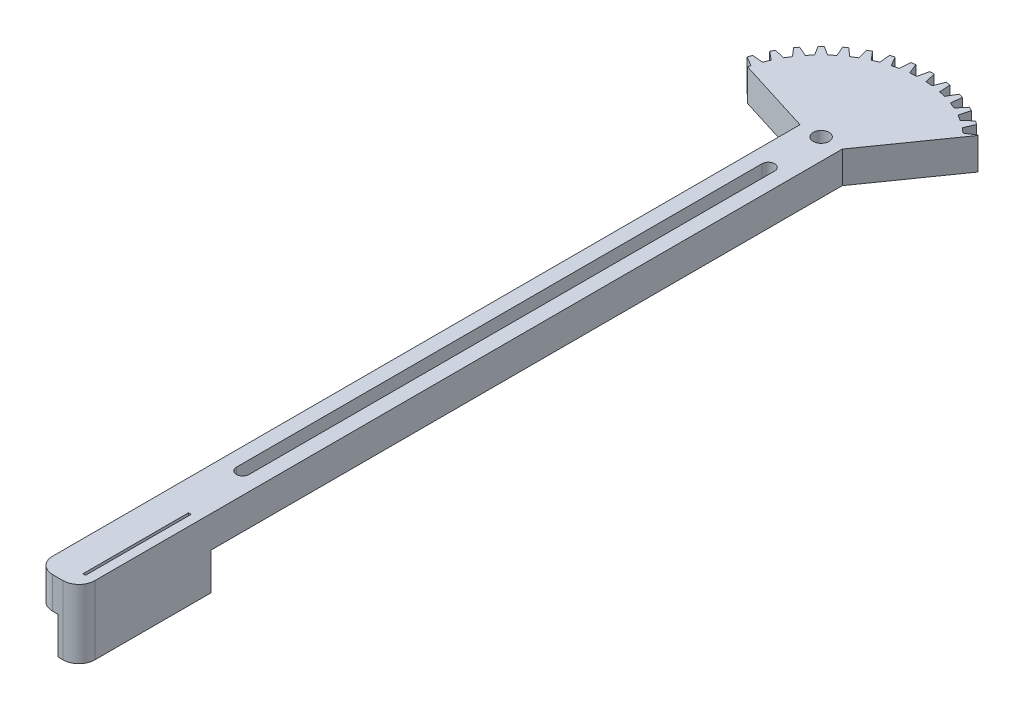
SolidWorks part; units mm, degrees
material "PBT General Purpose"
ref_plane "Front Plane" through (0, 0, 0) normal (0, 0, 1) x (1, 0, 0)
ref_plane "Top Plane" through (0, 0, 0) normal (0, 1, 0) x (1, 0, 0)
ref_plane "Right Plane" through (0, 0, 0) normal (1, 0, 0) x (0, 0, -1)
sketch "Sketch1" plane through (0, 0, 0) normal (0, 1, 0) x (1, 0, 0)
  circle A0 centre (0, 0) radius 21
  circle A1 centre (0, 0) radius 1.5
  dimension "D2" = 3
  dimension "D1" = 42
extrude "Boss-Extrude1" add sketch "Sketch1" along normal blind 6
sketch "Sketch2" plane through (0, 6, 0) normal (0, 1, 0) x (1, 0, 0)
  line L0 (0, 0) -> (0, 15.5) construction
  line L1 (0, 0) -> (-0.4123, 20.996) construction
  line L2 (0, 0) -> (-0.8702, 18.9801) construction
  line L3 (0, 0) -> (-1.4907, 18.9414) construction
  line L4 (-0.8702, 18.9801) -> (-0.4123, 20.996)
  line L5 (0.8702, 18.9801) -> (0.4123, 20.996)
  line L6 (-1.4907, 18.9414) -> (-1.7314, 22)
  line L7 (1.4907, 18.9414) -> (1.7314, 22)
  line L8 (-1.7314, 22) -> (1.7314, 22)
  arc A0 (-0.8702, 18.9801) -> (-1.4907, 18.9414) centre (0, 0) ccw
  circle A1 centre (0, 0) radius 21 construction
  arc A2 (0.4123, 20.996) -> (-0.4123, 20.996) centre (0, 0) ccw
  arc A3 (0.8702, 18.9801) -> (1.4907, 18.9414) centre (0, 0) cw
  dimension "D1" = 19
  dimension "D2" = 1.125
  dimension "D3" = 1.5
  dimension "D4" = 1.875
  dimension "D5" = 22
extrude "Cut-Extrude1" cut sketch "Sketch2" against normal up to next (6 mm away)
pattern_circular "CirPattern1" count 40 over 360 about axis through (0, 0, 0) along (0, 1, 0) of "Cut-Extrude1"
sketch "Sketch3" plane through (0, 6, 0) normal (0, 1, 0) x (1, 0, 0)
  line L0 (4, 0) -> (-4, 0) construction
  line L1 (0, 0) -> (0, 21.0096) construction
  line L2 (0, 0) -> (-26.0972, 6.5552) construction
  line L3 (-4, 0) -> (-20.3673, 5.1159)
  line L4 (-4, 0) -> (4, 0)
  line L6 (0, 0) -> (-7.8504, 27.559) construction
  line L7 (0, 0) -> (15.7913, 16.2954) construction
  line L8 (4, 0) -> (14.6142, 15.0807)
  arc A0 (-20.3673, 5.1159) -> (14.6142, 15.0807) centre (0, 0) ccw
  point P5 (0, 0)
  dimension "D3" = 21
  dimension "D1" = 8
  dimension "D2" = 60
  dimension "D4" = 15.9
  dimension "D5" = 120
extrude "Cut-Extrude2" cut sketch "Sketch3" against normal up to next
sketch "Sketch4" plane through (0, 0, 0) normal (0, -1, 0) x (1, 0, 0)
  line L0 (1.5, 0) -> (4, 0)
  line L1 (-4, 0) -> (-1.5, 0)
  line L2 (-4, 0) -> (-4, 141.5)
  line L3 (-1, 144.5) -> (1, 144.5)
  line L4 (4, 0) -> (4, 141.5)
  arc A0 (1.5, 0) -> (-1.5, 0) centre (0, 0) ccw
  arc A1 (-4, 141.5) -> (-1, 144.5) centre (-1, 141.5) cw
  arc A2 (1, 144.5) -> (4, 141.5) centre (1, 141.5) cw
  point P5 (0, 140)
  point P12 (0, 140)
  point P14 (0, 140)
  dimension "D5" = 3
  dimension "D1" = 4.5
  dimension "D3" = 140
extrude "Boss-Extrude2" add sketch "Sketch4" against normal up to surface (6 mm away) up to face at (-4.0836, 6, -14.6127)
sketch "Sketch5" plane through (0, 0, 0) normal (0, -1, 0) x (1, 0, 0)
  line L0 (-4, 119.5) -> (4, 119.5)
  line L1 (0, 119.5) -> (0, 144.5)
  line L32 (14.6142, -15.0807) -> (4, 0)
  line L33 (4, 0) -> (4, 141.5)
  line L34 (4, 0) -> (4, 141.5)
  line L35 (1, 144.5) -> (-1, 144.5)
  line L36 (-4, 0) -> (-18.455, -4.5182)
  line L37 (-18.32, -5.0376) -> (-20.0957, -6.096)
  line L38 (-19.8409, -6.8802) -> (-17.7822, -6.6928)
  line L39 (-17.3064, -7.8414) -> (-18.8947, -9.1646)
  line L40 (-18.5203, -9.8993) -> (-16.5163, -9.3921)
  line L41 (-15.8667, -10.4522) -> (-17.2284, -12.0075)
  line L42 (-16.7437, -12.6747) -> (-14.8437, -11.8602)
  line L43 (-14.0362, -12.8056) -> (-15.1379, -14.5548)
  line L44 (-14.5548, -15.1379) -> (-12.8056, -14.0362)
  line L45 (-11.8602, -14.8437) -> (-12.6747, -16.7437)
  line L46 (-12.0075, -17.2284) -> (-10.4522, -15.8667)
  line L47 (-9.3921, -16.5163) -> (-9.8993, -18.5203)
  line L48 (-9.1646, -18.8947) -> (-7.8414, -17.3064)
  line L49 (-6.6928, -17.7822) -> (-6.8802, -19.8409)
  line L50 (-6.096, -20.0957) -> (-5.0376, -18.32)
  line L51 (-3.8286, -18.6103) -> (-3.6917, -20.673)
  line L52 (-2.8773, -20.802) -> (-2.1097, -18.8825)
  line L53 (-0.8702, -18.9801) -> (-0.4123, -20.996)
  line L54 (0.4123, -20.996) -> (0.8702, -18.9801)
  line L55 (2.1097, -18.8825) -> (2.8773, -20.802)
  line L56 (3.6917, -20.673) -> (3.8286, -18.6103)
  line L57 (5.0376, -18.32) -> (6.096, -20.0957)
  line L58 (6.8802, -19.8409) -> (6.6928, -17.7822)
  line L59 (7.8414, -17.3064) -> (9.1646, -18.8947)
  line L60 (9.8993, -18.5203) -> (9.3921, -16.5163)
  line L61 (10.4522, -15.8667) -> (12.0075, -17.2284)
  line L62 (12.6747, -16.7437) -> (11.8602, -14.8437)
  line L63 (12.8056, -14.0362) -> (14.5548, -15.1379)
  line L97 (1, 144.5) -> (-1, 144.5)
  line L99 (-4, 141.5) -> (-4, 0)
  line L100 (-4, 141.5) -> (-4, 0)
  arc A28 (4, 141.5) -> (1, 144.5) centre (1, 141.5) ccw
  arc A29 (4, 141.5) -> (1, 144.5) centre (1, 141.5) ccw
  arc A31 (-20.0957, -6.096) -> (-19.8409, -6.8802) centre (0, 0) ccw
  arc A32 (-17.7822, -6.6928) -> (-17.3064, -7.8414) centre (0, 0) ccw
  arc A33 (-18.8947, -9.1646) -> (-18.5203, -9.8993) centre (0, 0) ccw
  arc A34 (-16.5163, -9.3921) -> (-15.8667, -10.4522) centre (0, 0) ccw
  arc A35 (-17.2284, -12.0075) -> (-16.7437, -12.6747) centre (0, 0) ccw
  arc A36 (-14.8437, -11.8602) -> (-14.0362, -12.8056) centre (0, 0) ccw
  arc A37 (-15.1379, -14.5548) -> (-14.5548, -15.1379) centre (0, 0) ccw
  arc A38 (-12.8056, -14.0362) -> (-11.8602, -14.8437) centre (0, 0) ccw
  arc A39 (-12.6747, -16.7437) -> (-12.0075, -17.2284) centre (0, 0) ccw
  arc A40 (-10.4522, -15.8667) -> (-9.3921, -16.5163) centre (0, 0) ccw
  arc A41 (-9.8993, -18.5203) -> (-9.1646, -18.8947) centre (0, 0) ccw
  arc A42 (-7.8414, -17.3064) -> (-6.6928, -17.7822) centre (0, 0) ccw
  arc A43 (-6.8802, -19.8409) -> (-6.096, -20.0957) centre (0, 0) ccw
  arc A44 (-5.0376, -18.32) -> (-3.8286, -18.6103) centre (0, 0) ccw
  arc A45 (-3.6917, -20.673) -> (-2.8773, -20.802) centre (0, 0) ccw
  arc A46 (-2.1097, -18.8825) -> (-0.8702, -18.9801) centre (0, 0) ccw
  arc A47 (-0.4123, -20.996) -> (0.4123, -20.996) centre (0, 0) ccw
  arc A48 (0.8702, -18.9801) -> (2.1097, -18.8825) centre (0, 0) ccw
  arc A49 (2.8773, -20.802) -> (3.6917, -20.673) centre (0, 0) ccw
  arc A50 (3.8286, -18.6103) -> (5.0376, -18.32) centre (0, 0) ccw
  arc A51 (6.096, -20.0957) -> (6.8802, -19.8409) centre (0, 0) ccw
  arc A52 (6.6928, -17.7822) -> (7.8414, -17.3064) centre (0, 0) ccw
  arc A53 (9.1646, -18.8947) -> (9.8993, -18.5203) centre (0, 0) ccw
  arc A54 (9.3921, -16.5163) -> (10.4522, -15.8667) centre (0, 0) ccw
  arc A55 (12.0075, -17.2284) -> (12.6747, -16.7437) centre (0, 0) ccw
  arc A56 (11.8602, -14.8437) -> (12.8056, -14.0362) centre (0, 0) ccw
  arc A57 (14.5548, -15.1379) -> (14.6142, -15.0807) centre (0, 0) ccw
  arc A87 (-1, 144.5) -> (-4, 141.5) centre (-1, 141.5) ccw
  arc A88 (-1, 144.5) -> (-4, 141.5) centre (-1, 141.5) ccw
  arc A90 (-18.455, -4.5182) -> (-18.32, -5.0376) centre (0, 0) ccw
  arc A91 (-18.455, -4.5182) -> (-18.32, -5.0376) centre (0, 0) ccw
  dimension "D2" = 25
  dimension "D1" = 0
extrude "Boss-Extrude3" add sketch "Sketch5" along normal blind 7 contours L34 A29 L97 L1 L0
sketch "Sketch7" plane through (0, -7, 0) normal (0, -1, 0) x (1, 0, 0)
  line L5 (0, 119.5) -> (4, 119.5) construction
  line L7 (1.75, 121.5) -> (2.25, 121.5)
  line L8 (1.75, 121.5) -> (1.75, 141.5)
  line L9 (1.75, 141.5) -> (2.25, 141.5)
  line L10 (2.25, 121.5) -> (2.25, 141.5)
  point P4 (2, 121.5)
  point P10 (2, 119.5)
  dimension "D1" = 2
  dimension "D2" = 0.5
  dimension "D3" = 20
extrude "Cut-Extrude4" cut sketch "Sketch7" against normal up to next
sketch "Sketch8" plane through (0, 0, 0) normal (0, -1, 0) x (1, 0, 0)
  line L0 (0, 10) -> (0, 109.5) construction
  line L1 (-1.2, 10) -> (-1.2, 109.5)
  line L2 (1.2, 10) -> (1.2, 109.5)
  line L3 (0, 119.5) -> (4, 119.5) construction
  arc A0 (-1.2, 10) -> (1.2, 10) centre (0, 10) ccw
  arc A1 (1.2, 109.5) -> (-1.2, 109.5) centre (0, 109.5) ccw
  point P3 (0, 59.75)
  dimension "D3" = 1.2
  dimension "D1" = 10
  dimension "D2" = 10
extrude "Cut-Extrude5" cut sketch "Sketch8" against normal up to next
equation "\"num_teeth\"= 40"
equation "\"D2@Sketch2\"=(1.5/6)*(360 / \"num_teeth\")*0.5"
equation "\"D3@Sketch2\"=(2/6)*(360 / \"num_teeth\")*0.5"
equation "\"D4@Sketch2\"=(2.5/6)*(360 / \"num_teeth\")*0.5"
equation "\"D1@CirPattern1\"=\"num_teeth\""
equation "\"teeth_angle_offset\"= 15.9deg"
equation "\"D4@Sketch3\"=\"teeth_angle_offset\""
equation "\"diameter\"= 40mm"
equation "\"D1@Sketch1\"=\"diameter\" + 2"
equation "\"D1@Sketch2\"=(\"diameter\" / 2) - 1"
equation "\"D3@Sketch3\"=(\"diameter\" / 2) + 1"
equation "\"teeth_fraction_required\"= 1 / 3"
equation "\"D5@Sketch3\"=360 * \"teeth_fraction_required\""
equation "\"D2@Sketch3\"=360 * \"teeth_fraction_required\" * 0.5"
equation "\"bar_length\"= 140mm"
equation "\"D3@Sketch4\"=\"bar_length\""
equation "\"D5@Sketch2\"=\"diameter\" / 2 + 2"
